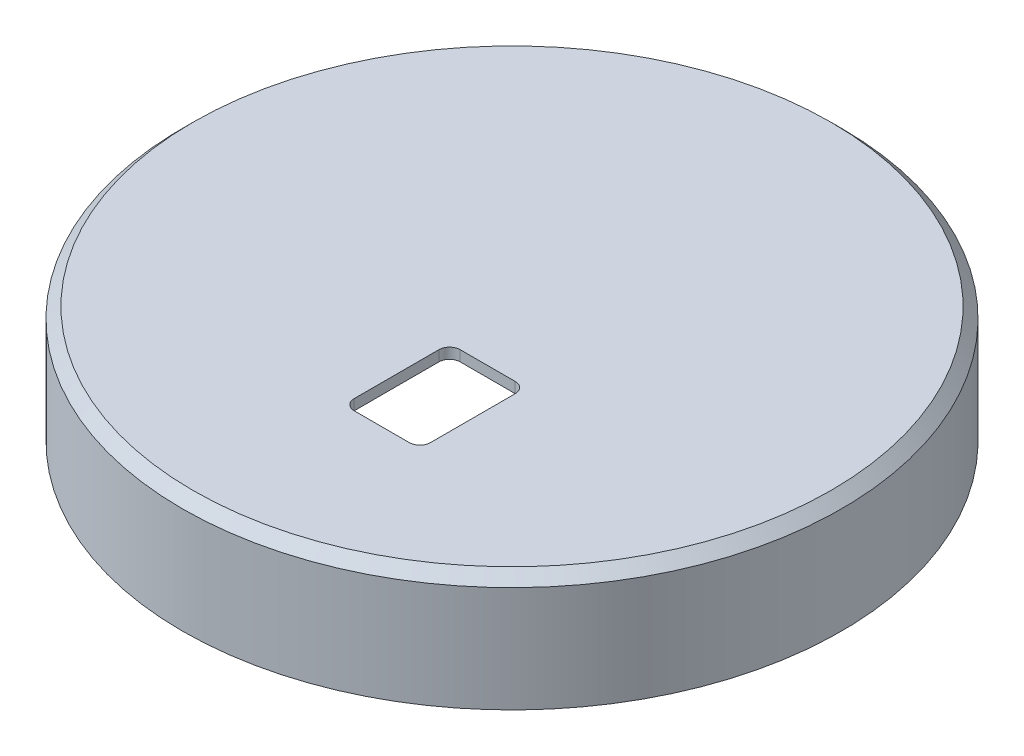
SolidWorks part; units mm, degrees
ref_plane "Ebene vorne" through (0, 0, 0) normal (0, 0, 1) x (1, 0, 0)
ref_plane "Ebene oben" through (0, 0, 0) normal (0, 1, 0) x (1, 0, 0)
ref_plane "Ebene rechts" through (0, 0, 0) normal (1, 0, 0) x (0, 0, -1)
sketch "Skizze1" plane through (0, 0, 0) normal (0, 1, 0) x (1, 0, 0)
  circle A0 centre (0, 0) radius 31.1127
  circle A1 centre (0, 0) radius 29.1127
  circle A2 centre (0, 0) radius 31.1127 construction
  dimension "D2" = 2
extrude "Aufsatz-Linear austragen1" add sketch "Skizze1" along normal blind 10
sketch "Skizze2" plane through (0, 10, 0) normal (0, 1, 0) x (1, 0, 0)
  circle A0 centre (0, 0) radius 31.1127
  circle A1 centre (0, 0) radius 31.1127 construction
extrude "Aufsatz-Linear austragen2" add sketch "Skizze2" along normal blind 1
sketch "Skizze3" plane through (0, 11, 0) normal (0, 1, 0) x (1, 0, 0)
  line L0 (0, 0) -> (-46.4213, 0) construction
  line L1 (-31.1127, 0) -> (-31.1127, 15.213) construction
  line L2 (0, 0) -> (0, 17.3597) construction
  line L3 (-27.1127, 3.75) -> (-30.8859, 3.75)
  line L4 (-27.1127, -3.75) -> (-30.8859, -3.75)
  line L5 (27.1127, -3.75) -> (30.8859, -3.75)
  line L6 (27.1127, 3.75) -> (30.8859, 3.75)
  line L7 (-30.8859, 3.75) -> (-34.1632, 0.7281)
  line L8 (-34.1632, 0.7281) -> (-30.8859, -3.75)
  line L9 (34.1632, 0.7281) -> (30.8859, -3.75)
  line L10 (30.8859, 3.75) -> (34.1632, 0.7281)
  circle A0 centre (-27.1127, 0) radius 2.75
  circle A2 centre (0, 0) radius 31.1127 construction
  circle A3 centre (27.1127, 0) radius 2.75
  arc A4 (-27.1127, 3.75) -> (-27.1127, -3.75) centre (-27.1127, 0) cw
  arc A5 (27.1127, 3.75) -> (27.1127, -3.75) centre (27.1127, 0) ccw
  dimension "D1" = 5.5
  dimension "D3" = 1
  dimension "D2" = 4
extrude "Schnitt-Linear austragen1" [suppressed] cut sketch "Skizze3" against normal through all
sketch "Skizze4" plane through (0, 10, 0) normal (0, -1, 0) x (1, 0, 0)
  line L0 (0, 0) -> (39.4101, 0) construction
  line L1 (31.1127, 0) -> (31.1127, 9.5037) construction
  line L2 (0, 0) -> (0, 10.4457) construction
  circle A0 centre (0, 0) radius 31.1127 construction
  circle A1 centre (28.3127, 0) radius 1.5 construction
  arc A2 (28.7664, 4.4771) -> (28.7664, -4.4771) centre (28.3127, 0) ccw
  circle A3 centre (0, 0) radius 29.1127 construction
  arc A4 (-28.7664, 4.4771) -> (-28.7664, -4.4771) centre (-28.3127, 0) cw
  dimension "D1" = 3
  dimension "D3" = 3
  dimension "D2" = 2.8
extrude "Aufsatz-Linear austragen3" add sketch "Skizze4" along normal up to surface (10 mm away) up to face at (0, 0, 31.1127)
sketch "Skizze5" plane through (0, 0, 0) normal (0, -1, 0) x (1, 0, 0)
  line L0 (0, 0) -> (40.9284, 0)
  line L1 (31.1127, 0) -> (31.1127, 7.0978) construction
  line L2 (0, 0) -> (0, 11.2853)
  circle A0 centre (27.7127, 0) radius 1.425
  circle A1 centre (0, 0) radius 31.1127 construction
  circle A2 centre (-27.7127, 0) radius 1.425
  dimension "D1" = 2.85
  dimension "D2" = 3.4
extrude "Schnitt-Linear austragen2" cut sketch "Skizze5" against normal blind 10 contours A2 | L0 A0 | L0 A0
sketch "Skizze6" plane through (0, 11, 0) normal (0, 1, 0) x (1, 0, 0)
  line L0 (0, 0) -> (0, -33.5463) construction
  line L1 (0.0919, -15.988) -> (7.2919, -15.988)
  line L2 (0.0919, -15.988) -> (0.0919, -5.988)
  line L3 (0.0919, -5.988) -> (7.2919, -5.988)
  line L4 (7.2919, -15.988) -> (7.2919, -5.988)
  line L5 (0.0919, -15.988) -> (7.2919, -5.988) construction
  line L6 (0.0919, -5.988) -> (7.2919, -15.988) construction
  line L7 (0, 0) -> (-45.5313, 0) construction
  point P0 (3.6919, -10.988)
  dimension "D1" = 10
  dimension "D2" = 7.2
  dimension "D3" = 3.6919
  dimension "D4" = 10.988
extrude "Schnitt-Linear austragen3" cut sketch "Skizze6" against normal blind 10
pattern_circular "Kreismuster1" count 2 every 90 about axis through (0, 0, 0) along (0, 1, 0) of "Aufsatz-Linear austragen3", "Schnitt-Linear austragen2"
chamfer "Fase1" distance 1 angle 45 1 edges at (0, 11, 31.1127)
fillet "Verrundung1" radius 2 8 edges at (-4.4771, 5, -28.7664) (4.4771, 5, -28.7664) (28.7664, 5, -4.4771) (28.7664, 5, 4.4771) (-28.7664, 5, -4.4771) (-28.7664, 5, 4.4771) (-4.4771, 5, 28.7664) (4.4771, 5, 28.7664)
fillet "Verrundung2" radius 1 4 edges at (7.2919, 10.5, 15.988) (7.2919, 10.5, 5.988) (0.0919, 10.5, 5.988) (0.0919, 10.5, 15.988)
chamfer "Fase2" distance 1 angle 45 16 edges at (20.5858, 10, -20.5858) (5.2162, 10, -28.1278) (28.1278, 10, -5.2162) (0, 10, -23.8127) (23.8127, 10, 0) (-5.2162, 10, -28.1278) (28.1278, 10, 5.2162) (-20.5858, 10, -20.5858) (20.5858, 10, 20.5858) (-28.1278, 10, -5.2162) (5.2162, 10, 28.1278) (-23.8127, 10, 0) (0, 10, 23.8127) (-28.1278, 10, 5.2162) (-5.2162, 10, 28.1278) (-20.5858, 10, 20.5858)
sketch "Skizze7" plane through (0, 11, 0) normal (0, 1, 0) x (1, 0, 0)
  line L0 (-28.0492, 4.6425) -> (29.405, 4.6425) construction
  line L1 (-21.9498, -0.641) -> (22.5714, -0.641) construction
  line L2 (-24.747, -9.0601) -> (-2.8399, -9.0601) construction
  line L3 (-22.2995, -14.8987) -> (-2.6029, -14.8987) construction
  text T0 "<b>OpenAstroTech</b>" font "Century Gothic" height in points 18
  text T1 "<b>OAG v1.0</b>"
  text T2 "<b>FL 183mm</b>" font "Century Gothic" height 3.2
  text T3 "<b>\"/px  2.9</b>" font "Century Gothic" height 3.2
extrude "Schnitt-Linear austragen4" [suppressed] cut sketch "Skizze7" against normal blind 0.2
